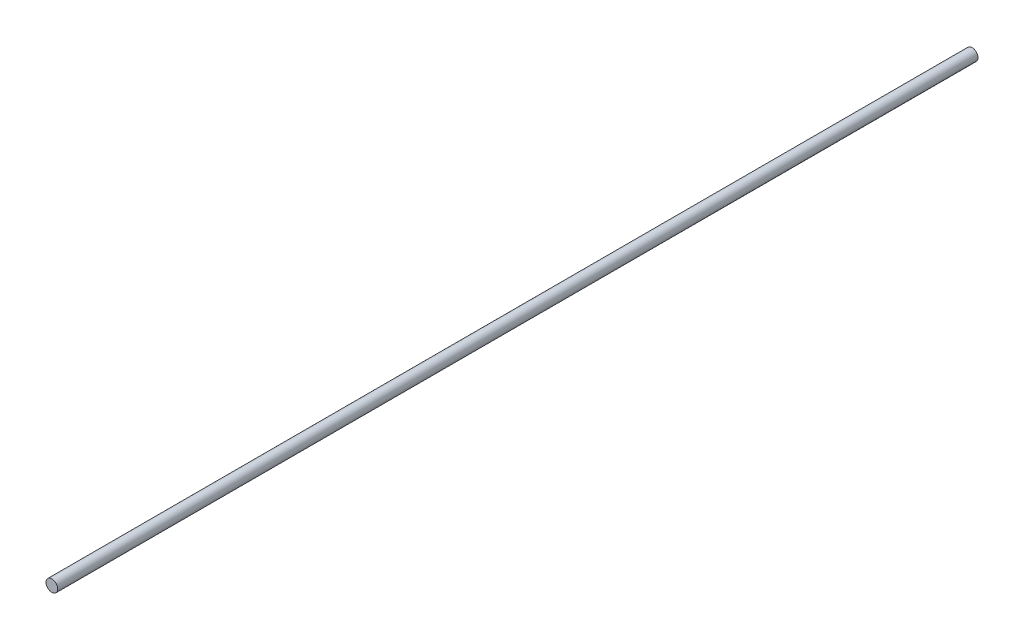
SolidWorks part; units mm, degrees
ref_plane "Plan de face" through (0, 0, 0) normal (0, 0, 1) x (1, 0, 0)
ref_plane "Plan de dessus" through (0, 0, 0) normal (0, 1, 0) x (1, 0, 0)
ref_plane "Plan de droite" through (0, 0, 0) normal (1, 0, 0) x (0, 0, -1)
sketch "Esquisse1" plane through (0, 0, 0) normal (0, 0, 1) x (1, 0, 0)
  circle A0 centre (0, 0) radius 4
  dimension "D1" = 8
extrude "Boss.-Extru.1" add sketch "Esquisse1" along normal blind 628
